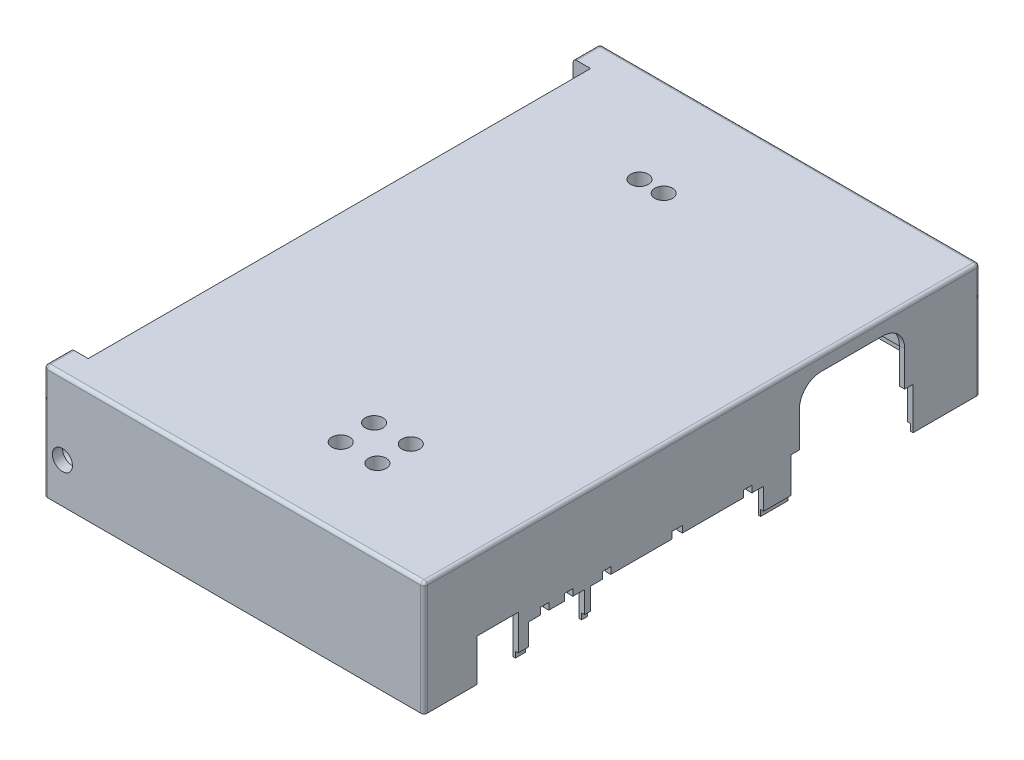
SolidWorks part; units mm, degrees
ref_plane "Спереди" through (0, 0, 0) normal (0, 0, 1) x (1, 0, 0)
ref_plane "Сверху" through (0, 0, 0) normal (0, 1, 0) x (1, 0, 0)
ref_plane "Справа" through (0, 0, 0) normal (1, 0, 0) x (0, 0, -1)
sketch "Эскиз1" plane through (0, 0, 0) normal (0, 1, 0) x (1, 0, 0)
  line L0 (-54.2, 83.1) -> (-61.2, 83.1)
  line L1 (-54.2, -83.1) -> (54.2, -83.1)
  line L3 (-54.2, 83.1) -> (54.2, 83.1)
  line L4 (54.2, -83.1) -> (54.2, 83.1)
  line L5 (-61.2, 83.1) -> (-61.2, -83.1)
  line L6 (-61.2, -83.1) -> (-54.2, -83.1)
  point P0 (0, 0)
sketch "Эскиз2" plane through (0, 0, 0) normal (0, -1, 0) x (1, 0, 0)
  line L0 (-54.2, 83.1) -> (54.2, 83.1)
  line L1 (54.2, 83.1) -> (54.2, -83.1)
  line L2 (54.2, -83.1) -> (-54.2, -83.1)
  line L5 (-54.2, -81.5) -> (52.6, -81.5)
  line L6 (52.6, -81.5) -> (52.6, 81.5)
  line L7 (52.6, 81.5) -> (-54.2, 81.5)
  line L10 (-59.4, 81.5) -> (-54.2, 81.5)
  line L11 (-59.4, 81.5) -> (-59.4, 83.1)
  line L17 (-59.4, 83.1) -> (-54.2, 83.1)
  line L19 (-59.4, -81.5) -> (-54.2, -81.5)
  line L20 (-59.4, -81.5) -> (-59.4, -83.1)
  line L21 (-59.4, -83.1) -> (-54.2, -83.1)
extrude "Бобышка-Вытянуть2" add sketch "Эскиз2" along normal blind 35
sketch "Эскиз3" plane through (0, 0, 0) normal (0, -1, 0) x (1, 0, 0)
  line L1 (52.6, 81.5) -> (43, 81.5)
  line L2 (52.6, 81.5) -> (52.6, 71.9)
  line L3 (52.6, 71.9) -> (43, 71.9)
  line L4 (43, 81.5) -> (43, 71.9)
  line L5 (52.6, -81.5) -> (43, -81.5)
  line L6 (52.6, -81.5) -> (52.6, -71.9)
  line L7 (52.6, -71.9) -> (43, -71.9)
  line L8 (43, -81.5) -> (43, -71.9)
extrude "Бобышка-Вытянуть3" add sketch "Эскиз3" along normal blind 35
sketch "Эскиз8" plane through (0, 0, 0) normal (0, -1, 0) x (1, 0, 0)
  line L15 (-61.2, 81.5) -> (43, 81.5) construction
  line L26 (-49.4, 81.5) -> (-49.4, 75.1)
  line L29 (-59.4, 75.1) -> (-49.4, 75.1)
  line L32 (-59.4, 81.5) -> (-59.4, 75.1)
  line L35 (-59.4, 81.5) -> (-49.4, 81.5)
extrude "Бобышка-Вытянуть4" add sketch "Эскиз8" along normal blind 35
mirror "Зеркальное отражение1" about plane through (0, 0, 0) normal (0, 0, 1) of "Бобышка-Вытянуть4"
sketch "Эскиз10" plane through (0, -35, 0) normal (0, -1, 0) x (1, 0, 0)
  line L1 (-59.4, 83.1) -> (-59.4, 75.1)
  line L12 (54.2, -83.1) -> (54.2, 83.1)
  line L19 (53.5, 82.4) -> (53.5, -82.4)
  line L22 (-59.4, 75.1) -> (-58.7, 75.1)
  line L24 (-59.4, 75.1) -> (-49.4, 75.1) construction
  line L25 (-58.7, 75.1) -> (-58.7, 82.4)
  line L26 (-58.7, 82.4) -> (53.5, 82.4)
  line L27 (54.2, 83.1) -> (-59.4, 83.1)
  line L28 (-59.4, -75.1) -> (-58.7, -75.1)
  line L29 (-59.4, -75.1) -> (-49.4, -75.1) construction
  line L30 (-58.7, -75.1) -> (-58.7, -82.4)
  line L31 (-59.4, -75.1) -> (-59.4, -83.1)
  line L32 (-59.4, -83.1) -> (54.2, -83.1)
  line L33 (53.5, -82.4) -> (-58.7, -82.4)
extrude "Бобышка-Вытянуть5" add sketch "Эскиз10" along normal blind 2
sketch "Эскиз34" plane through (0, 0, -83.1) normal (0, 0, -1) x (-1, 0, 0)
  circle A1 centre (53.9, -25) radius 3
  point P8 (53.9, -25)
hole_wizard "Отверстие2" positions "Эскиз34" profile "Эскиз69" legacy
sketch "Эскиз69" plane through (-53.9, -25, -83.1) normal (1, 0, 0) x (0, 1, 0)
  line L0 (0, 0) -> (0, 9)
  line L1 (0, 9) -> (1.55, 9)
  line L2 (1.55, 9) -> (1.55, 4.45)
  line L3 (1.55, 4.45) -> (3, 3)
  line L4 (3, 3) -> (3, 0)
  line L5 (3, 0) -> (0, 0)
  line L6 (0, -6.13) -> (0, 109.2824) construction
  line L7 (-1.55, 4.45) -> (-3, 3) construction
  line L8 (0, 9) -> (-1.55, 9) construction
  dimension "Диаметр" = 3.1
  dimension "Глубина" = 9
  dimension "Диа. рассверливания" = 6
  dimension "Глуб. рассверливания" = 3
  dimension "Угол рассверл." = 90
mirror "Зеркальное отражение2" about plane through (0, 0, 0) normal (0, 0, 1) of "Отверстие2"
fillet "Скругление1" radius 2 2 edges at (43, -17.5, 71.9) (43, -17.5, -71.9)
sketch "Эскиз11" plane through (0, -35, 0) normal (0, -1, 0) x (1, 0, 0)
  circle A0 centre (47.8, 76.7) radius 1.45
  circle A1 centre (47.8, -76.7) radius 1.45
extrude "Вырез-Вытянуть7" cut sketch "Эскиз11" against normal blind 8
sketch "Эскиз24" plane through (54.2, 0, 0) normal (1, 0, 0) x (0, 0, -1)
  line L0 (-67.1158, -24.4586) -> (-54.9158, -24.4586)
  line L2 (83.1, -37) -> (-83.1, -37) construction
  line L3 (-54.95, -37) -> (-67.2, -37)
  line L16 (26.6008, -24.4586) -> (26.6008, -37)
  line L18 (26.6008, -37) -> (63.1, -37)
  line L19 (63.1, -37) -> (63.1, -24.4586) construction
  line L20 (63.1, -37) -> (63.1, -24.4586)
  line L42 (-54.95, -37) -> (-54.9, -37)
  line L44 (-54.9, -37) -> (-54.9, -24.4586)
  line L45 (-54.9, -24.4586) -> (-54.9158, -24.4586)
  line L46 (-67.2, -37) -> (-67.2, -24.4586)
  line L47 (-67.2, -24.4586) -> (-67.1158, -24.4586)
  line L52 (-33.275, -37) -> (18.425, -37)
  line L53 (-51.8, -37) -> (-35.1, -37)
  line L57 (-29.775, -26.5) -> (-27.275, -26.5)
  line L58 (-33.275, -37) -> (-33.275, -28.5)
  line L59 (-33.275, -28.5) -> (-29.775, -28.5)
  line L60 (-29.775, -28.5) -> (-29.775, -26.5)
  line L61 (-27.275, -26.5) -> (-27.275, -28.5)
  line L62 (-27.275, -28.5) -> (-8.975, -28.5)
  line L65 (18.425, -28.5) -> (18.425, -37)
  line L66 (12.425, -28.5) -> (-5.875, -28.5)
  line L67 (12.425, -26.5) -> (12.425, -28.5)
  line L70 (18.425, -28.5) -> (14.925, -28.5)
  line L71 (14.925, -28.5) -> (14.925, -26.5)
  line L72 (14.925, -26.5) -> (12.425, -26.5)
  line L75 (-8.975, -28.5) -> (-8.975, -26.5)
  line L76 (-8.975, -26.5) -> (-5.875, -26.5)
  line L77 (-5.875, -26.5) -> (-5.875, -28.5)
  line L78 (-51.8, -37) -> (-51.8, -28.5)
  line L79 (-51.8, -28.5) -> (-48.3, -28.5)
  line L80 (-48.3, -28.5) -> (-48.3, -26.5)
  line L81 (-48.3, -26.5) -> (-45.8, -26.5)
  line L82 (-45.8, -26.5) -> (-45.8, -28.5)
  line L83 (-35.1, -37) -> (-35.1, -28.5)
  line L84 (-35.1, -28.5) -> (-38.6014, -28.5)
  line L85 (-38.6014, -28.5) -> (-38.6014, -26.5)
  line L86 (-38.6014, -26.5) -> (-41.1014, -26.5)
  line L87 (-41.1014, -26.5) -> (-41.1014, -28.5)
  line L88 (-41.1014, -28.5) -> (-45.8, -28.5)
  line L91 (29.1008, -24.4586) -> (26.6008, -24.4586)
  line L92 (63.1, -24.4586) -> (60.6, -24.4586)
  line L94 (29.1008, -24.4586) -> (29.1008, -13.9586)
  line L95 (35.6352, -7.4241) -> (54.0656, -7.4241)
  line L96 (60.6, -24.4586) -> (60.6, -13.9586)
  arc A2 (29.1008, -13.9586) -> (35.6352, -7.4241) centre (35.6352, -13.9586) cw
  arc A3 (60.6, -13.9586) -> (54.0656, -7.4241) centre (54.0656, -13.9586) ccw
  dimension "D1" = 3.5
  dimension "D2" = 2.5
  dimension "D3" = 2.5
  dimension "D4" = 18.3
  dimension "D5" = 2
extrude "Вырез-Вытянуть17" cut sketch "Эскиз24" against normal blind 1.6
sketch "Эскиз77" plane through (0, -35, 0) normal (0, -1, 0) x (1, 0, 0)
  line L0 (52.6, 54.9) -> (53.5, 54.9)
  line L1 (53.5, 54.9) -> (53.5, 51.8)
  line L2 (53.5, 51.8) -> (52.6, 51.8)
  line L3 (52.6, 51.8) -> (52.6, 54.9)
  line L5 (52.6, 35.1) -> (53.5, 35.1)
  line L6 (52.6, 35.1) -> (52.6, 33.275)
  line L7 (52.6, 33.275) -> (53.5, 33.275)
  line L8 (53.5, 35.1) -> (53.5, 33.275)
  line L9 (52.6, -18.425) -> (53.5, -18.425)
  line L10 (52.6, -18.425) -> (52.6, -26.6008)
  line L11 (52.6, -26.6008) -> (53.5, -26.6008)
  line L12 (53.5, -18.425) -> (53.5, -26.6008)
extrude "Бобышка-Вытянуть15" add sketch "Эскиз77" along normal blind 2
sketch "Эскиз78" plane through (0, -37, 0) normal (0, -1, 0) x (1, 0, 0)
  line L1 (54.2, 35.1) -> (53.3, 35.1)
  line L2 (54.2, 35.1) -> (54.2, 33.275)
  line L3 (54.2, 33.275) -> (53.3, 33.275)
  line L4 (53.3, 35.1) -> (53.3, 33.275)
  line L5 (54.2, -18.425) -> (53.3, -18.425)
  line L6 (54.2, -18.425) -> (54.2, -26.6008)
  line L7 (54.2, -26.6008) -> (53.3, -26.6008)
  line L8 (53.3, -18.425) -> (53.3, -26.6008)
  line L9 (54.2, 54.9) -> (53.3, 54.9)
  line L10 (54.2, 54.9) -> (54.2, 51.8)
  line L11 (54.2, 51.8) -> (53.3, 51.8)
  line L12 (53.3, 54.9) -> (53.3, 51.8)
  dimension "D1" = 0.9
extrude "Вырез-Вытянуть20" cut sketch "Эскиз78" against normal blind 2
sketch "Эскиз79" plane through (53.3, 0, 0) normal (1, 0, 0) x (0, 0, -1)
  line L1 (-54.9, -37) -> (-51.8, -37)
  line L2 (-54.9, -37) -> (-54.9, -36.8)
  line L3 (-54.9, -36.8) -> (-51.8, -36.8)
  line L4 (-51.8, -37) -> (-51.8, -36.8)
  line L5 (-35.1, -37) -> (-33.275, -37)
  line L6 (-35.1, -37) -> (-35.1, -36.8)
  line L7 (-35.1, -36.8) -> (-33.275, -36.8)
  line L8 (-33.275, -37) -> (-33.275, -36.8)
  line L9 (18.425, -37) -> (26.6008, -37)
  line L10 (18.425, -37) -> (18.425, -36.8)
  line L11 (18.425, -36.8) -> (26.6008, -36.8)
  line L12 (26.6008, -37) -> (26.6008, -36.8)
extrude "Вырез-Вытянуть21" cut sketch "Эскиз79" against normal blind 0.7
extrude "Вырез-Вытянуть18" cut sketch "Эскиз1" against normal blind 4.5
sketch "Эскиз32" plane through (0, -4.5, 0) normal (0, 1, 0) x (1, 0, 0)
  line L0 (-59.4, 83.1) -> (54.2, 83.1)
  line L4 (54.2, 83.1) -> (54.2, -83.1)
  line L5 (-59.4, 83.1) -> (-59.4, -83.1)
  line L6 (-59.4, -83.1) -> (54.2, -83.1)
extrude "Бобышка-Вытянуть6" add sketch "Эскиз32" along normal blind 1.6
sketch "Эскиз33" plane through (0, -2.9, 0) normal (0, 1, 0) x (1, 0, 0)
  line L1 (-61.2, 75.1) -> (-54.2, 75.1)
  line L2 (-61.2, 75.1) -> (-61.2, -75.1)
  line L3 (-61.2, -75.1) -> (-54.2, -75.1)
  line L4 (-54.2, 75.1) -> (-54.2, -75.1)
extrude "Вырез-Вытянуть19" cut sketch "Эскиз33" against normal blind 1.6
sketch "Эскиз35" plane through (0, -4.5, 0) normal (0, -1, 0) x (1, 0, 0)
  circle A0 centre (5.1693, 49.0001) radius 3.65
extrude "Бобышка-Вытянуть7" add sketch "Эскиз35" along normal blind 5 contours A0
sketch "Эскиз70" plane through (0, -9.5, 0) normal (0, -1, 0) x (-1, 0, 0)
  point P0 (-5.1693, -49.0001)
hole_wizard "Отверстие3" positions "Эскиз70" profile "Эскиз71" legacy end condition through all
sketch "Эскиз71" plane through (5.1693, -9.5, 49.0001) normal (1, 0, 0) x (0, 0, -1)
  line L0 (0, 0) -> (0, 6.6)
  line L1 (0, 6.6) -> (2.65, 6.6)
  line L2 (2.65, 6.6) -> (2.65, 0.5)
  line L3 (2.65, 0.5) -> (3.15, 0)
  line L4 (3.15, 0) -> (0, 0)
  line L5 (0, -6.4453) -> (0, 115.525) construction
  line L6 (-2.65, 0.5) -> (-3.15, 0) construction
  dimension "Диаметр" = 5.3
  dimension "Глубина" = 6.6
  dimension "Угол зенк." = 90
  dimension "Диа. зенковки" = 6.3
sketch "Эскиз48" plane through (0, -4.5, 0) normal (0, -1, 0) x (1, 0, 0)
  circle A0 centre (-18.2143, -53.7251) radius 3.65
extrude "Бобышка-Вытянуть8" add sketch "Эскиз48" along normal blind 5
sketch "Эскиз53" plane through (0, -4.5, 0) normal (0, -1, 0) x (1, 0, 0)
  circle A1 centre (16.1443, 49.0001) radius 3.65
extrude "Бобышка-Вытянуть9" add sketch "Эскиз53" along normal blind 5
sketch "Эскиз59" plane through (0, -4.5, 0) normal (0, -1, 0) x (1, 0, 0)
  circle A0 centre (-10.975, -53.7251) radius 3.65
extrude "Бобышка-Вытянуть12" add sketch "Эскиз59" along normal blind 5
sketch "Эскиз62" plane through (0, -4.5, 0) normal (0, -1, 0) x (1, 0, 0)
  line L1 (1.9216, 56.7339) -> (8.4232, 61.2317)
  line L3 (8.4216, 56.7317) -> (1.9232, 61.2339)
  line L4 (12.8982, 61.2301) -> (19.3966, 56.7279)
  line L6 (19.3982, 61.2279) -> (12.9, 56.75)
sketch "Эскиз64" plane through (0, -4.5, 0) normal (0, -1, 0) x (1, 0, 0)
  line L0 (1.9216, 56.7339) -> (8.4232, 61.2317) construction
  circle A0 centre (5.1724, 58.9828) radius 3.65
extrude "Бобышка-Вытянуть13" add sketch "Эскиз64" along normal blind 5
sketch "Эскиз72" plane through (0, -4.5, 0) normal (0, -1, 0) x (1, 0, 0)
  circle A0 centre (16.1443, 58.9828) radius 3.65
extrude "Бобышка-Вытянуть14" add sketch "Эскиз72" along normal blind 5
sketch "Эскиз75" plane through (0, -9.5, 0) normal (0, -1, 0) x (-1, 0, 0)
  point P0 (-16.1443, -58.9828)
  point P3 (-16.1443, -49.0001)
  point P6 (-5.1724, -58.9828)
  point P9 (10.975, 53.7251)
  point P12 (18.2143, 53.7251)
hole_wizard "Отверстие5" positions "Эскиз75" profile "Эскиз76" legacy end condition through all
sketch "Эскиз76" plane through (16.1443, -9.5, 58.9828) normal (1, 0, 0) x (0, 0, -1)
  line L0 (0, 0) -> (0, 6.6)
  line L1 (0, 6.6) -> (2.65, 6.6)
  line L2 (2.65, 6.6) -> (2.65, 0.5)
  line L3 (2.65, 0.5) -> (3.15, 0)
  line L4 (3.15, 0) -> (0, 0)
  line L5 (0, -6.4453) -> (0, 115.525) construction
  line L6 (-2.65, 0.5) -> (-3.15, 0) construction
  dimension "Диаметр" = 5.3
  dimension "Глубина" = 6.6
  dimension "Угол зенк." = 90
  dimension "Диа. зенковки" = 6.3
fillet "Скругление2" radius 1 9 edges at (54.2, -2.9, 0) (-59.4, -2.9, -79.1) (-59.4, -2.9, 79.1) (-2.6, -2.9, 83.1) (-2.6, -2.9, -83.1) (-59.4, -19.95, -83.1) (-59.4, -19.95, 83.1) (54.2, -19.95, 83.1) (54.2, -19.95, -83.1)
sketch "Эскиз81" plane through (0, -4.5, 0) normal (0, -1, 0) x (1, 0, 0)
  line L1 (22.6, 81.5) -> (32.6, 81.5)
  line L2 (22.6, 81.5) -> (22.6, -81.5)
  line L3 (22.6, -81.5) -> (32.6, -81.5)
  line L4 (32.6, 81.5) -> (32.6, -81.5)
  line L5 (-49.4, 81.5) -> (-39.4, 81.5)
  line L6 (-49.4, 81.5) -> (-49.4, -81.5)
  line L7 (-49.4, -81.5) -> (-39.4, -81.5)
  line L8 (-39.4, 81.5) -> (-39.4, -81.5)
extrude "Бобышка-Вытянуть16" add sketch "Эскиз81" along normal blind 6
